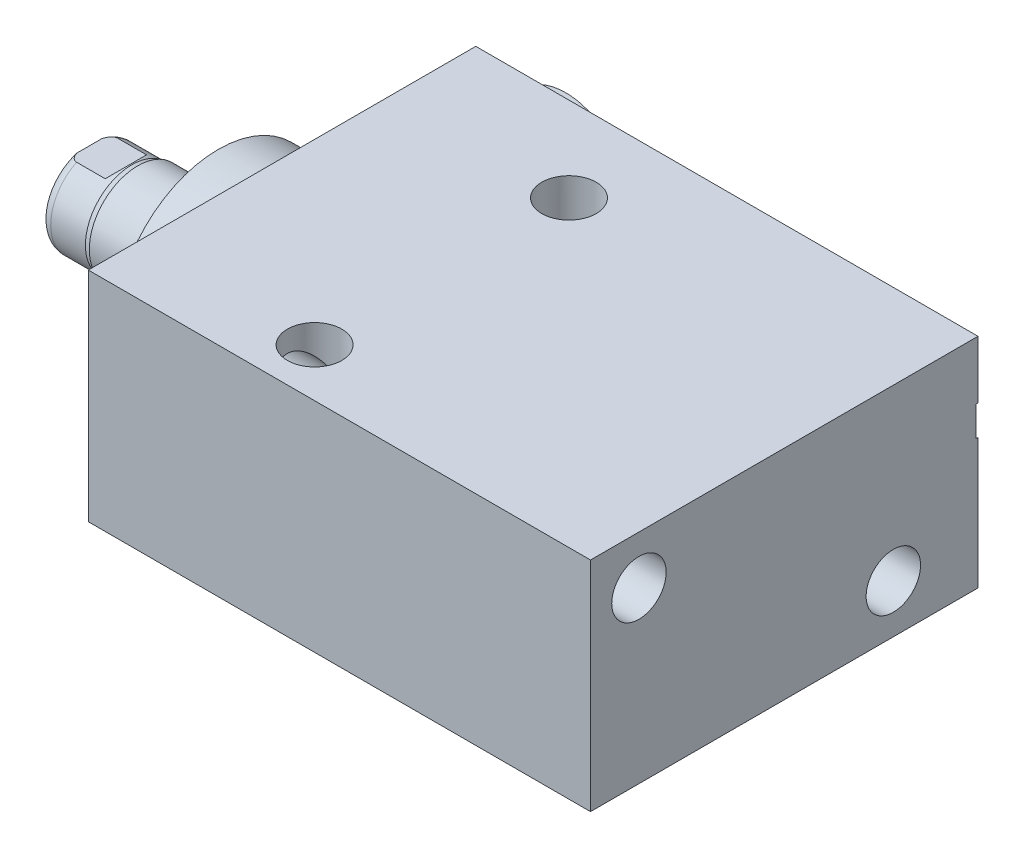
SolidWorks part; units mm, degrees
material "Alloy Steel"
ref_plane "Front Plane" through (0, 0, 0) normal (0, 0, 1) x (1, 0, 0)
ref_plane "Top Plane" through (0, 0, 0) normal (0, 1, 0) x (1, 0, 0)
ref_plane "Right Plane" through (0, 0, 0) normal (1, 0, 0) x (0, 0, -1)
ref_plane "Plane1" through (0, 0, 0) normal (1, 0, 0) x (0, 0, -1)
sketch "Sketch1" plane through (0, 0, 0) normal (1, 0, 0) x (0, 0, -1)
  line L0 (-23.0124, 14.2875) -> (27.7876, 14.2875)
  line L1 (27.7876, 14.2875) -> (27.7876, -14.2875)
  line L2 (27.7876, -14.2875) -> (-23.0124, -14.2875)
  line L3 (-23.0124, -14.2875) -> (-23.0124, 14.2875)
  line L4 (0, -24.4475) -> (0, 24.4475) construction
  dimension "D1" = 28.575
  dimension "D2" = 14.2875
  dimension "D3" = 50.8
  dimension "D4" = 23.0124
extrude "Extrude1" add sketch "Sketch1" along normal blind 65.8368
ref_plane "Plane12" through (0, 4.7625, 0) normal (0, 1, 0) x (-1, 0, 0)
sketch "S2D0002" plane through (0, 4.7625, 0) normal (0, 1, 0) x (-1, 0, 0)
  line L0 (-15.7099, -27.5336) -> (-19.05, -27.5336)
  line L1 (-15.7099, -27.5336) -> (-15.1673, -24.9809)
  line L2 (-15.1673, -24.9809) -> (-14.5034, -24.317)
  line L3 (-14.5034, -24.317) -> (-14.5034, -13.5636)
  line L4 (-14.5034, -13.5636) -> (-9.525, -13.5636)
  line L5 (-9.525, -13.5636) -> (-9.525, -27.7876)
  line L6 (-9.525, -19.1384) -> (-9.525, 0.6985) construction
  line L7 (0, -27.7876) -> (0, 23.0124) construction
  line L8 (-19.05, -27.7876) -> (-19.05, -27.5336)
  line L9 (-65.8368, -27.7876) -> (0, -27.7876) construction
  line L10 (-19.05, -27.7876) -> (-9.525, -27.7876)
  dimension "D1" = 14.224
  dimension "D2" = 9.525
  dimension "D3" = 9.9568
  dimension "D4" = 45
  dimension "D5" = 12.3698
  dimension "D6" = 12
  dimension "D7" = 2.5527
  dimension "D8" = 0.254
  dimension "D9" = 19.05
revolve "Cut-Revolve1" cut sketch "S2D0002" angle 360 about L6
ref_plane "Plane13" through (0, 4.7625, 0) normal (0, 1, 0) x (-1, 0, 0)
sketch "Sketch3" plane through (41.148, 4.7625, -25.146) normal (0, 1, 0) x (1, 0, 0)
  line L0 (21.5519, 2.3876) -> (24.892, 2.3876)
  line L1 (21.5519, 2.3876) -> (21.0093, -0.1651)
  line L2 (21.0093, -0.1651) -> (20.3454, -0.829)
  line L3 (20.3454, -0.829) -> (20.3454, -11.5824)
  line L4 (20.3454, -11.5824) -> (15.367, -11.5824)
  line L5 (15.367, -11.5824) -> (15.367, 2.6416)
  line L6 (15.367, -21.9564) -> (15.367, 0.6985) construction
  line L7 (-41.148, 2.6416) -> (-41.148, -48.1584) construction
  line L8 (24.892, 2.6416) -> (24.892, 2.3876)
  line L9 (24.6888, 2.6416) -> (-41.148, 2.6416) construction
  line L10 (24.892, 2.6416) -> (15.367, 2.6416)
  dimension "D1" = 14.224
  dimension "D2" = 56.515
  dimension "D3" = 9.9568
  dimension "D4" = 45
  dimension "D5" = 12
  dimension "D6" = 12.3698
  dimension "D7" = 2.5527
  dimension "D8" = 0.254
  dimension "D9" = 19.05
revolve "Cut-Revolve2" cut sketch "Sketch3" angle 360 about L6
sketch "Sketch5" plane through (0, 0, 0) normal (-1, 0, 0) x (0, 0, 1)
  circle A0 centre (0, 0) radius 13.5001
  dimension "D1" = 27.0002
extrude "Extrude2" add sketch "Sketch5" along normal blind 5.969
ref_plane "Plane5" through (0, 0, 0) normal (0, -1, 0) x (0, 0, 1)
sketch "Sketch6" plane through (0, 0, 0) normal (0, -1, 0) x (0, 0, 1)
  line L0 (0, 5.969) -> (-6.35, 5.969)
  line L1 (-6.35, 5.969) -> (-6.35, 22.86)
  line L2 (-6.35, 22.86) -> (0, 22.86)
  line L3 (0, 22.86) -> (0, 5.969)
  line L4 (0, -5.7546) -> (0, 21.1709) construction
  line L5 (13.5001, 5.969) -> (-13.5001, 5.969) construction
  line L6 (23.0124, -65.8368) -> (-27.7876, -65.8368) construction
  dimension "D1" = 88.6968
  dimension "D2" = 12.7
revolve "Revolve1" add sketch "Sketch6" angle 360 about L4
ref_plane "Plane6" through (-18.5113, 3.2639, 0) normal (0, 0, 1) x (0, 1, 0)
sketch "S2D0001" plane through (-18.5113, 3.2639, 0) normal (0, 0, 1) x (0, 1, 0)
  line L0 (-0.7112, 2.7869) -> (-0.7112, -11.6533)
  line L1 (-3.2639, -13.1871) -> (-0.7112, -11.6533)
  line L2 (0.1905, 4.3487) -> (-3.2639, 4.3487)
  line L3 (-3.2639, 4.3487) -> (-3.2639, -13.1871)
  line L4 (-0.7112, 2.7869) -> (0.1905, 4.3487)
  line L5 (-3.2639, -18.5113) -> (-3.2639, 2.765) construction
  line L6 (3.0861, 4.3487) -> (-9.6139, 4.3487) construction
  dimension "D1" = 30
  dimension "D2" = 6.9088
  dimension "D3" = 5.1054
  dimension "D4" = 16.002
  dimension "D5" = 59
revolve "Cut-Revolve4" cut sketch "S2D0001" angle 360 about L5
ref_plane "Plane7" through (0, 0, 0) normal (0, 1, 0) x (0, 0, -1)
sketch "Sketch8" plane through (0, 0, 0) normal (0, 1, 0) x (0, 0, -1)
  line L0 (-6.35, 16.5354) -> (-6.096, 17.2974)
  line L1 (-6.096, 17.2974) -> (-6.096, 21.844)
  line L2 (0, 12.6594) -> (0, 20.8178) construction
  line L3 (-6.35, 16.5354) -> (-6.35, 22.86)
  line L4 (-5.7079, 22.86) -> (-6.35, 22.86)
  line L5 (6.35, 22.86) -> (-6.35, 22.86) construction
  line L6 (-6.35, 22.86) -> (-6.35, 5.969) construction
  arc A0 (-5.7079, 22.86) -> (-6.096, 21.844) centre (-4.572, 21.844) ccw
  dimension "D2" = 1.524
  dimension "D1" = 12.192
  dimension "D3" = 1.016
  dimension "D4" = 0.762
  dimension "D5" = 5.5626
revolve "Cut-Revolve5" cut sketch "Sketch8" angle 360 about L2
ref_plane "Plane11" through (0, 0, 0) normal (0, 0, -1) x (0, -1, 0)
sketch "Sketch12" plane through (0, 0, 0) normal (0, 0, -1) x (0, -1, 0)
  line L0 (5.461, 22.86) -> (5.461, 18.0848)
  line L1 (5.461, 18.0848) -> (6.096, 17.4498)
  line L2 (-5.461, 22.86) -> (-5.461, 18.0848)
  line L3 (-5.461, 18.0848) -> (-6.096, 17.4498)
  line L4 (5.461, 22.86) -> (6.096, 22.86)
  line L5 (0, 13.7262) -> (0, 20.767) construction
  line L6 (-6.096, 17.4498) -> (-6.096, 22.86)
  line L8 (6.096, 17.2974) -> (6.096, 21.844) construction
  line L9 (6.096, 17.4498) -> (6.096, 22.86)
  line L10 (-5.461, 22.86) -> (-6.096, 22.86)
  line L12 (5.7079, 22.86) -> (-5.7079, 22.86) construction
  dimension "D1" = 10.922
  dimension "D2" = 4.7752
  dimension "D3" = 45
extrude "Cut-Extrude4" cut sketch "Sketch12" against normal mid plane 60.96
sketch "Sketch13" plane through (0, 0, -27.5336) normal (0, 0, -1) x (-1, 0, 0)
  circle A0 centre (-9.525, 4.7625) radius 7.874
  circle A1 centre (-9.525, 4.7625) radius 6.1849 construction
  dimension "D1" = 15.748
extrude "Extrude3" add sketch "Sketch13" along normal blind 2.54
hole_wizard "Hole1" positions "Sketch15" profile "Sketch14" legacy end condition up to next
sketch "Sketch15" plane through (0, 0, 0) normal (-1, 0, 0) x (0, 0, 1)
  line L0 (0, 0) -> (-29.9914, 0) construction
  line L1 (0, 0) -> (0, 25.7648) construction
  point P0 (-16.6878, -7.9248)
  point P11 (16.6624, 7.9502)
  dimension "D1" = 7.9248
  dimension "D2" = 16.6878
  dimension "D3" = 15.875
  dimension "D4" = 33.3502
sketch "Sketch14" plane through (0, -7.9248, -16.6878) normal (0, 1, 0) x (0, 0, 1)
  line L0 (0, 0) -> (0, 65.8368)
  line L1 (0, 65.8368) -> (3.5687, 65.8368)
  line L2 (3.5687, 65.8368) -> (3.5687, 0)
  line L3 (3.5687, 0) -> (0, 0)
  line L4 (0, 110) -> (0, -10) construction
  dimension "Diameter" = 7.1374
  dimension "Depth" = 65.8368
hole_wizard "Hole2" positions "Sketch17" profile "Sketch16" legacy
sketch "Sketch17" plane through (0, 14.2875, 0) normal (0, 1, 0) x (-1, 0, 0)
  line L0 (0, 0) -> (-59.3363, 0) construction
  line L1 (0, -27.7876) -> (0, 23.0124) construction
  point P0 (-23.3172, -16.6878)
  point P9 (-23.3172, 16.6624)
  dimension "D1" = 33.3502
  dimension "D2" = 23.3172
  dimension "D3" = 16.6878
sketch "Sketch16" plane through (23.3172, 14.2875, -16.6878) normal (1, 0, 0) x (0, 0, 1)
  line L0 (0, 0) -> (0, 28.575)
  line L1 (0, 28.575) -> (3.5687, 28.575)
  line L2 (3.5687, 28.575) -> (3.5687, 0)
  line L3 (3.5687, 0) -> (0, 0)
  line L4 (0, 110) -> (0, -10) construction
  dimension "Diameter" = 7.1374
  dimension "Depth" = 28.575
